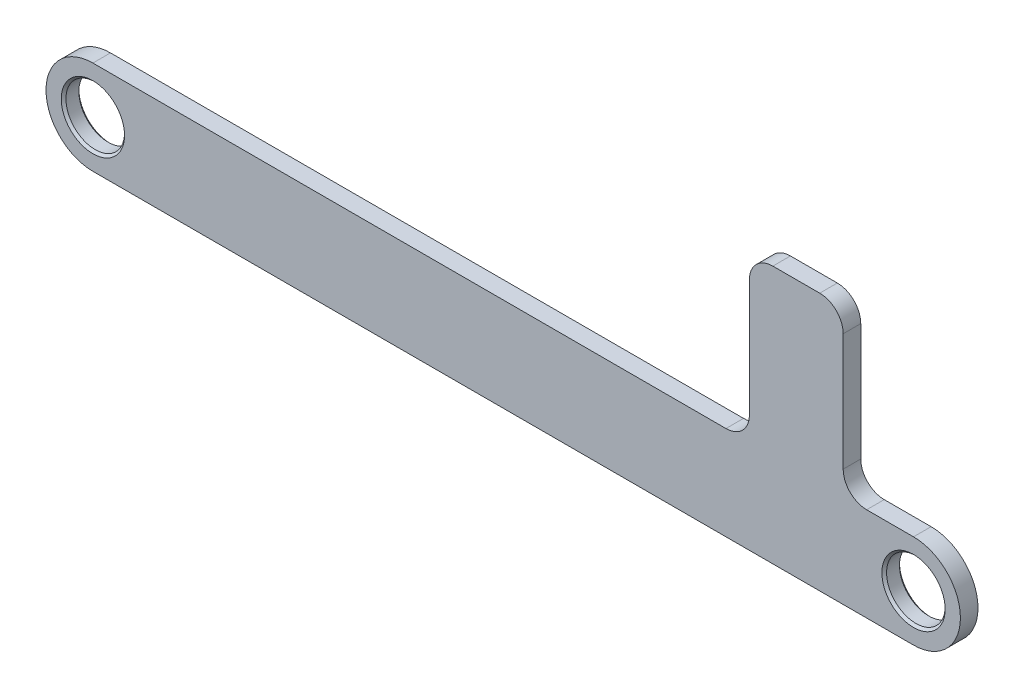
SolidWorks part; units mm, degrees
ref_plane "Plan de face" through (0, 0, 0) normal (0, 0, 1) x (1, 0, 0)
ref_plane "Plan de dessus" through (0, 0, 0) normal (0, 1, 0) x (1, 0, 0)
ref_plane "Plan de droite" through (0, 0, 0) normal (1, 0, 0) x (0, 0, -1)
sketch "Esquisse1" plane through (0, 0, 0) normal (0, 0, 1) x (1, 0, 0)
  line L0 (0, 0) -> (-70, 0) construction
  line L1 (-70, 4) -> (-14, 4)
  line L2 (-14, 18) -> (-6, 18)
  line L3 (-6, 18) -> (-6, 4)
  line L4 (-6, 4) -> (0, 4)
  line L5 (0, -4) -> (-70, -4)
  line L6 (-14, 4) -> (-14, 18)
  arc A0 (0, -4) -> (0, 4) centre (0, 0) ccw
  arc A1 (-70, 4) -> (-70, -4) centre (-70, 0) ccw
  circle A2 centre (-70, 0) radius 2.5
  circle A3 centre (0, 0) radius 2.5
  dimension "D1" = 5
  dimension "D2" = 4
  dimension "D3" = 70
  dimension "D5" = 6
  dimension "D4" = 8
  dimension "D6" = 22
extrude "Extrusion1" add sketch "Esquisse1" along normal mid plane 1.5
fillet "Congé1" radius 2 4 edges at (-14, 4, 0) (-14, 18, 0) (-6, 18, 0) (-6, 4, 0)
chamfer "Chanfrein1" distance 0.2 angle 45 4 edges at (-67.5, 0, -0.75) (-67.5, 0, 0.75) (2.5, 0, -0.75) (2.5, 0, 0.75)
